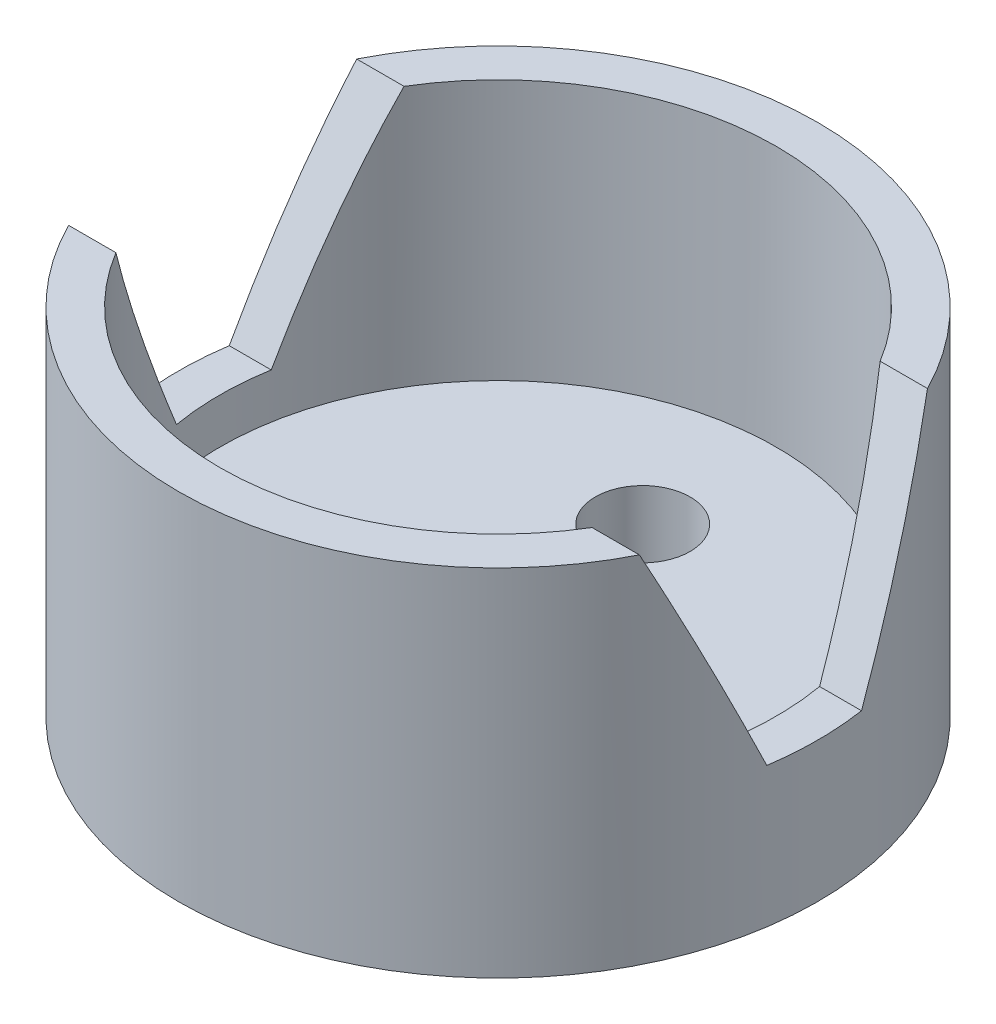
SolidWorks part; units mm, degrees
ref_plane "Спереди" through (0, 0, 0) normal (0, 0, 1) x (1, 0, 0)
ref_plane "Сверху" through (0, 0, 0) normal (0, 1, 0) x (1, 0, 0)
ref_plane "Справа" through (0, 0, 0) normal (1, 0, 0) x (0, 0, -1)
sketch "Эскиз1" plane through (0, 0, 0) normal (0, 1, 0) x (1, 0, 0)
  circle A0 centre (0, 0) radius 13.5
  dimension "D1" = 27
extrude "Бобышка-Вытянуть1" add sketch "Эскиз1" along normal blind 15
sketch "Эскиз2" plane through (0, 15, 0) normal (0, 1, 0) x (1, 0, 0)
  circle A0 centre (0, 0) radius 11.75
  dimension "D1" = 23.5
extrude "Вырез-Вытянуть1" cut sketch "Эскиз2" against normal blind 11
sketch "Эскиз3" plane through (0, 4, 0) normal (0, 1, 0) x (1, 0, 0)
  circle A0 centre (0, 6.1084) radius 2
  point P2 (0, 6.1084)
extrude "Вырез-Вытянуть2" cut sketch "Эскиз3" against normal through all
sketch "Эскиз4" plane through (0, 0, 0) normal (1, 0, 0) x (0, 0, -1)
  line L0 (0, 0) -> (0, 5.9075) construction
  line L2 (2, 5.9075) -> (-2, 5.9075)
  line L3 (-2, 5.9075) -> (-6.0831, 15)
  line L4 (13.5, 15) -> (-13.5, 15) construction
  line L5 (2, 5.9075) -> (6.0831, 15)
  line L6 (6.0831, 15) -> (-6.0831, 15)
  point P7 (0, 5.9075)
  dimension "D1" = 4
extrude "Вырез-Вытянуть3" cut sketch "Эскиз4" against normal through all both and the other way through all
